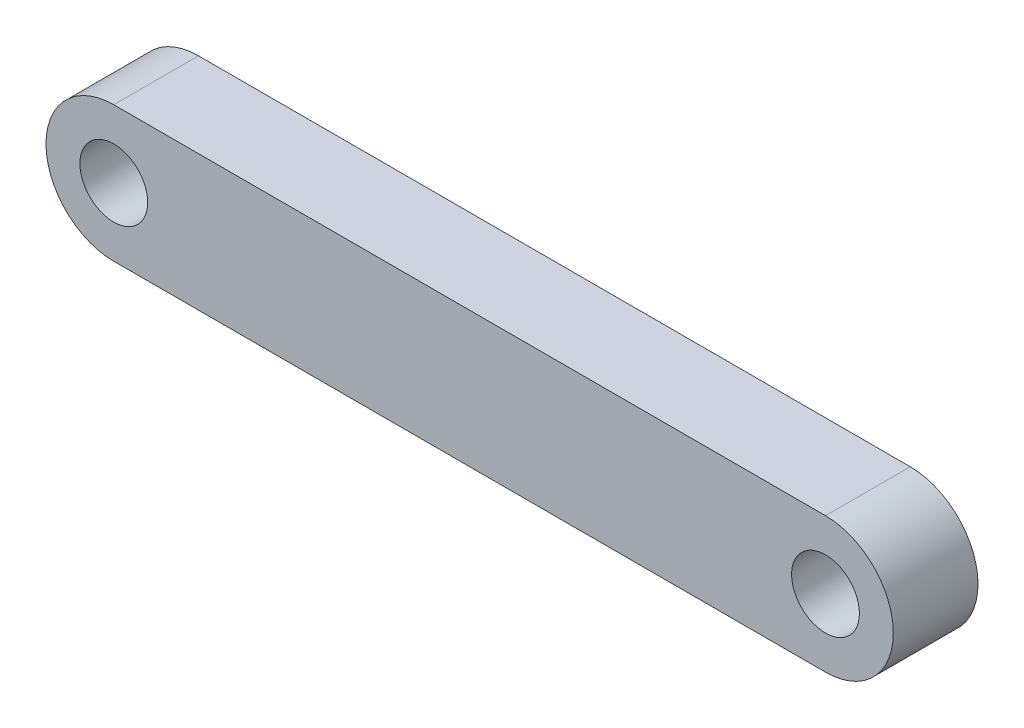
SolidWorks part; units mm, degrees
material "ABS"
ref_plane "Front Plane" through (0, 0, 0) normal (0, 0, 1) x (1, 0, 0)
ref_plane "Top Plane" through (0, 0, 0) normal (0, 1, 0) x (1, 0, 0)
ref_plane "Right Plane" through (0, 0, 0) normal (1, 0, 0) x (0, 0, -1)
sketch "Sketch1" plane through (0, 0, 0) normal (0, 0, 1) x (1, 0, 0)
  line L0 (0, 0) -> (42, 0) construction
  line L1 (0, 4) -> (42, 4)
  line L2 (0, -4) -> (42, -4)
  arc A0 (0, 4) -> (0, -4) centre (0, 0) ccw
  arc A1 (42, -4) -> (42, 4) centre (42, 0) ccw
  point P3 (21, 0)
  dimension "D2" = 4
  dimension "D1" = 42
extrude "Boss-Extrude1" add sketch "Sketch1" along normal mid plane 5
sketch "Sketch2" plane through (0, 0, 2.5) normal (0, 0, 1) x (1, 0, 0)
  circle A0 centre (42, 0) radius 2
  circle A1 centre (0, 0) radius 2
  dimension "D1" = 4
  dimension "D2" = 4
extrude "Cut-Extrude1" cut sketch "Sketch2" against normal through all
